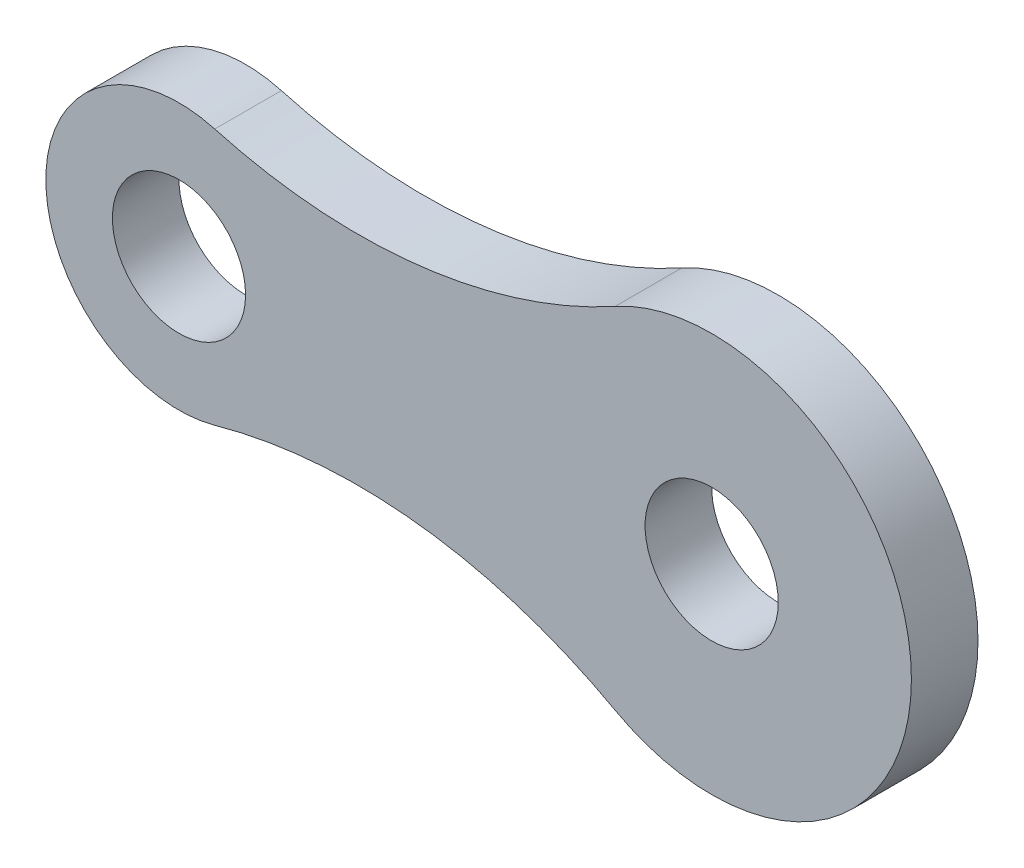
SolidWorks part; units mm, degrees
ref_plane "Front Plane" through (0, 0, 0) normal (0, 0, 1) x (1, 0, 0)
ref_plane "Top Plane" through (0, 0, 0) normal (0, 1, 0) x (1, 0, 0)
ref_plane "Right Plane" through (0, 0, 0) normal (1, 0, 0) x (0, 0, -1)
sketch "Sketch1" plane through (0, 0, 0) normal (0, 0, 1) x (1, 0, 0)
  line L0 (0, 0) -> (15.6673, 0) construction
  arc A0 (6.8263, 24.4655) -> (6.8263, -24.4655) centre (0, 0) ccw
  arc A1 (83.1994, -33.3621) -> (83.1994, 33.3621) centre (101.6, 0) ccw
  circle A2 centre (0, 0) radius 12.7
  circle A3 centre (101.6, 0) radius 12.7
  arc A4 (83.1994, -33.3621) -> (6.8263, -24.4655) centre (34.1313, -122.3277) ccw
  arc A5 (6.8263, 24.4655) -> (83.1994, 33.3621) centre (34.1313, 122.3277) ccw
  dimension "D1" = 50.8
  dimension "D3" = 76.2
  dimension "D4" = 25.4
  dimension "D5" = 25.4
  dimension "D6" = 203.2
  dimension "D7" = 203.2
  dimension "D2" = 101.6
extrude "Boss-Extrude1" add sketch "Sketch1" along normal blind 12.7
